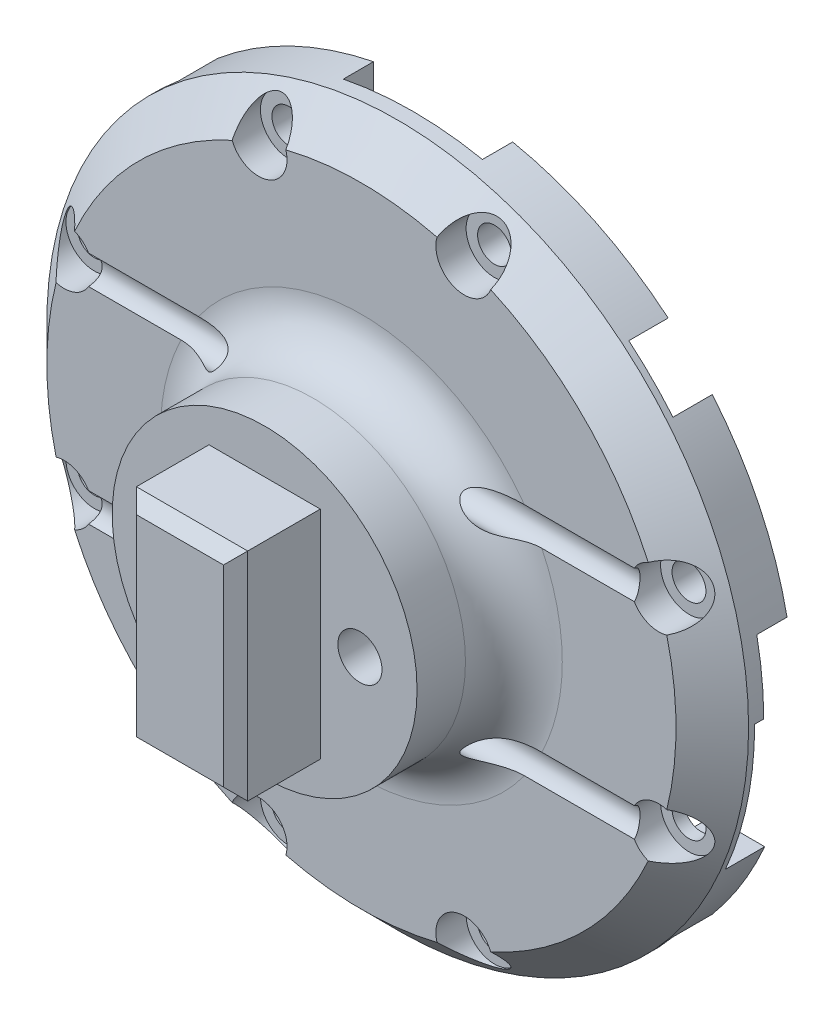
SolidWorks part; units mm, degrees
ref_plane "Front Plane" through (0, 0, 0) normal (0, 0, 1) x (1, 0, 0)
ref_plane "Top Plane" through (0, 0, 0) normal (0, 1, 0) x (1, 0, 0)
ref_plane "Right Plane" through (0, 0, 0) normal (1, 0, 0) x (0, 0, -1)
sketch "Sketch1" plane through (0, 0, 0) normal (0, 0, 1) x (1, 0, 0)
  circle A0 centre (0, 0) radius 29
  dimension "D1" = 58
extrude "Boss-Extrude1" add sketch "Sketch1" along normal blind 6.75
sketch "Sketch3" plane through (0, 0, 0) normal (0, 0, -1) x (-1, 0, 0)
  line L1 (-22.25, -22.25) -> (22.25, -22.25)
  line L2 (-22.25, -22.25) -> (-22.25, 22.25)
  line L3 (-22.25, 22.25) -> (22.25, 22.25)
  line L4 (22.25, -22.25) -> (22.25, 22.25)
  line L5 (-22.25, -22.25) -> (22.25, 22.25) construction
  line L6 (-22.25, 22.25) -> (22.25, -22.25) construction
  point P0 (0, 0)
  dimension "D1" = 44.5
extrude "Cut-Extrude1" cut sketch "Sketch3" against normal blind 3.25
sketch "Sketch4" plane through (0, 0, 6.75) normal (0, 0, 1) x (1, 0, 0)
  circle A0 centre (0, 0) radius 12.6
  dimension "D1" = 25.2
extrude "Boss-Extrude2" add sketch "Sketch4" along normal blind 8
fillet "Fillet1" radius 4 1 edges at (12.6, 0, 6.75)
sketch "Sketch5" plane through (0, 0, 14.75) normal (0, 0, 1) x (1, 0, 0)
  line L0 (0, 8.8489) -> (0, -6.8993) construction
  circle A0 centre (-7.875, 0) radius 1.825
  circle A1 centre (7.875, 0) radius 1.825
  dimension "D1" = 3.65
  dimension "D2" = 15.75
extrude "Cut-Extrude2" cut sketch "Sketch5" against normal through all
sketch "Sketch6" plane through (0, 0, 14.75) normal (0, 0, 1) x (1, 0, 0)
  line L1 (-4.6, 8.95) -> (4.6, 8.95)
  line L2 (-4.6, 8.95) -> (-4.6, -8.95)
  line L3 (-4.6, -8.95) -> (4.6, -8.95)
  line L4 (4.6, 8.95) -> (4.6, -8.95)
  line L5 (-4.6, 8.95) -> (4.6, -8.95) construction
  line L6 (-4.6, -8.95) -> (4.6, 8.95) construction
  point P0 (0, 0)
  dimension "D1" = 9.2
  dimension "D2" = 17.9
extrude "Boss-Extrude3" add sketch "Sketch6" along normal blind 7
chamfer "Chamfer1" distance 1 angle 45 4 edges at (0, -8.95, 21.75) (4.6, 0, 21.75) (0, 8.95, 21.75) (-4.6, 0, 21.75)
sketch "Sketch7" plane through (0, 0, 3.25) normal (0, 0, -1) x (-1, 0, 0)
  circle A0 centre (-7.875, 0) radius 3.25
  circle A1 centre (7.875, 0) radius 3.25
  dimension "D1" = 6.5
extrude "Cut-Extrude3" cut sketch "Sketch7" against normal blind 2.5
fillet "Fillet2" radius 1.5 2 edges at (-11.125, 0, 3.25) (4.625, 0, 3.25)
chamfer "Chamfer2" distance 3 angle 45 1 edges at (29, 0, 6.75)
sketch "Sketch9" plane through (0, 0, 0) normal (1, 0, 0) x (0, 0, -1)
  line L0 (-26.5723, 0) -> (15.7273, 0) construction
  line L2 (-6.75, 16.6) -> (-6.75, -16.6) construction
  circle A0 centre (-7.25, 8.5) radius 1.3
  circle A1 centre (-7.25, -8.5) radius 1.3
  point P7 (-5.3, 7.2531)
  point P8 (-5.8751, 7.2387)
  point P9 (-7.2865, 7.7985)
  point P12 (-6.75, 3.5352)
  dimension "D1" = 2.6
  dimension "D2" = 17
  dimension "D3" = 0.5
extrude "Cut-Extrude5" cut sketch "Sketch9" against normal through all both and the other way through all
sketch "Sketch10" plane through (0, 0, 0) normal (0, 0, -1) x (-1, 0, 0)
  line L0 (5.75, -22.0007) -> (5.75, -34.0342)
  line L1 (22.0007, 5.75) -> (34.0342, 5.75)
  line L2 (22.0007, 5.75) -> (22.0007, -5.75)
  line L3 (22.0007, -5.75) -> (34.0342, -5.75)
  line L4 (34.0342, 5.75) -> (34.0342, -5.75)
  line L5 (5.75, -22.0007) -> (-5.75, -22.0007)
  line L6 (-5.75, -22.0007) -> (-5.75, -34.0342)
  line L7 (5.75, -34.0342) -> (-5.75, -34.0342)
  line L8 (-22.0007, -5.75) -> (-34.0342, -5.75)
  line L9 (-22.0007, -5.75) -> (-22.0007, 5.75)
  line L10 (-22.0007, 5.75) -> (-34.0342, 5.75)
  line L11 (-34.0342, -5.75) -> (-34.0342, 5.75)
  line L12 (-5.75, 22.0007) -> (-5.75, 34.0342)
  line L13 (-5.75, 22.0007) -> (5.75, 22.0007)
  line L14 (5.75, 22.0007) -> (5.75, 34.0342)
  line L15 (-5.75, 34.0342) -> (5.75, 34.0342)
  point P4 (22.0007, 0)
  point P21 (0, 0)
  dimension "D1" = 11.5
  dimension "D2" = 4
extrude "Cut-Extrude6" cut sketch "Sketch10" against normal blind 2.5
sketch "Sketch11" plane through (0, 0, 0) normal (0, 0, -1) x (-1, 0, 0)
  line L0 (-36.6727, 0) -> (0, 0) construction
  circle A0 centre (0, 0) radius 26 construction
  circle A1 centre (-24.5713, 8.5) radius 1.4
  circle A2 centre (-24.5713, -8.5) radius 1.4
  circle A3 centre (-8.5, 24.5713) radius 1.4
  circle A4 centre (8.5, 24.5713) radius 1.4
  circle A5 centre (24.5713, 8.5) radius 1.4
  circle A6 centre (24.5713, -8.5) radius 1.4
  circle A7 centre (8.5, -24.5713) radius 1.4
  circle A8 centre (-8.5, -24.5713) radius 1.4
  point P8 (24.1404, 9.6562)
  point P9 (-24.4531, 8.8344)
  point P10 (24.4819, -8.7541)
  point P23 (0, 0)
  dimension "D1" = 52
  dimension "D3" = 2.8
  dimension "D4" = 17
  dimension "D2" = 4
extrude "Cut-Extrude7" cut sketch "Sketch11" against normal through all
sketch "Sketch12" plane through (0, 0, 6.75) normal (0, 0, 1) x (1, 0, 0)
  circle A0 centre (-24.5713, 8.5) radius 2.35
  circle A1 centre (-24.5713, -8.5) radius 2.35
  circle A2 centre (8.5, 24.5713) radius 2.35
  circle A3 centre (-8.5, 24.5713) radius 2.35
  circle A4 centre (24.5713, -8.5) radius 2.35
  circle A5 centre (24.5713, 8.5) radius 2.35
  circle A6 centre (-8.5, -24.5713) radius 2.35
  circle A7 centre (8.5, -24.5713) radius 2.35
  point P21 (0, 0)
  dimension "D1" = 4.7
  dimension "D2" = 4
extrude "Cut-Extrude8" cut sketch "Sketch12" against normal blind 2.5
sketch "Sketch13" plane through (0, 0, 3.25) normal (0, 0, -1) x (-1, 0, 0)
  line L0 (-22.25, 18.5994) -> (-22.25, -18.5994) construction
  line L1 (-22.15, 14.75) -> (-15.65, 14.75)
  line L2 (-22.15, 14.75) -> (-22.15, 8.25)
  line L3 (-22.15, 8.25) -> (-15.65, 8.25)
  line L4 (-15.65, 14.75) -> (-15.65, 8.25)
  line L5 (18.5994, 22.25) -> (-18.5994, 22.25) construction
  line L6 (14.75, 22.15) -> (14.75, 15.65)
  line L7 (14.75, 22.15) -> (8.25, 22.15)
  line L8 (8.25, 22.15) -> (8.25, 15.65)
  line L9 (14.75, 15.65) -> (8.25, 15.65)
  line L10 (22.15, -14.75) -> (15.65, -14.75)
  line L11 (22.15, -14.75) -> (22.15, -8.25)
  line L12 (22.15, -8.25) -> (15.65, -8.25)
  line L13 (15.65, -14.75) -> (15.65, -8.25)
  line L14 (-14.75, -22.15) -> (-14.75, -15.65)
  line L15 (-14.75, -22.15) -> (-8.25, -22.15)
  line L16 (-8.25, -22.15) -> (-8.25, -15.65)
  line L17 (-14.75, -15.65) -> (-8.25, -15.65)
  point P23 (0, 0)
  dimension "D1" = 0.1
  dimension "D2" = 7.5
  dimension "D4" = 6.5
  dimension "D3" = 4
extrude "Cut-Extrude9" cut sketch "Sketch13" against normal blind 2.25
chamfer "Chamfer5" distance 1 angle 45 12 edges at (-14.75, 18.9, 3.25) (-11.5, 15.65, 3.25) (-8.25, 18.9, 3.25) (14.75, -18.9, 3.25) (11.5, -15.65, 3.25) (8.25, -18.9, 3.25) (-18.9, -8.25, 3.25) (-15.65, -11.5, 3.25) (-18.9, -14.75, 3.25) (18.9, 8.25, 3.25) (15.65, 11.5, 3.25) (18.9, 14.75, 3.25)
sketch "Sketch14" plane through (0, 0, 0) normal (0, 0, -1) x (-1, 0, 0)
  line L1 (-35.1198, 0) -> (-19.2322, 0)
  line L2 (-35.1198, 0) -> (-35.1198, -11.6)
  line L3 (-35.1198, -11.6) -> (-19.2322, -11.6)
  line L4 (-19.2322, 0) -> (-19.2322, -11.6)
  dimension "D1" = 11.6
extrude "Cut-Extrude10" cut sketch "Sketch14" against normal up to surface (3.25 mm away) up to face at (18.4, 11.5, 3.25)
sketch "Sketch15" plane through (0, 0, 6.75) normal (0, 0, 1) x (1, 0, 0)
  line L0 (0, 0) -> (11.6673, 11.6673) construction
  line L1 (0, 0) -> (36.7921, 0) construction
  circle A0 centre (11.6673, 11.6673) radius 12.5
  circle A1 centre (0, 0) radius 29 construction
  dimension "D2" = 25
  dimension "D1" = 45
